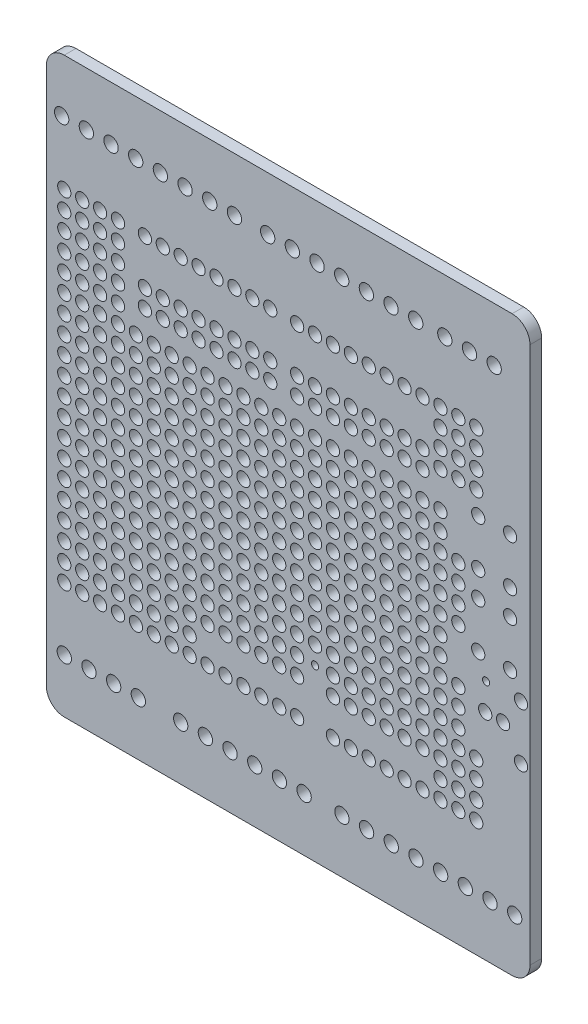
SolidWorks part; units mm, degrees
ref_plane "Front Plane" through (0, 0, 0) normal (0, 0, 1) x (1, 0, 0)
ref_plane "Top Plane" through (0, 0, 0) normal (0, 1, 0) x (1, 0, 0)
ref_plane "Right Plane" through (0, 0, 0) normal (1, 0, 0) x (0, 0, -1)
sketch "Model" plane through (0, 0, 0) normal (0, 0, 1) x (1, 0, 0)
  line L0 (2.54, 0) -> (66.04, 0)
  line L1 (68.58, 2.54) -> (68.58, 78.74)
  line L2 (0, 2.54) -> (0, 78.74)
  line L3 (2.54, 81.28) -> (66.04, 81.28)
  line L4 (48.91, 7.62) -> (45.41, 7.62) construction
  line L5 (45.41, 7.62) -> (41.91, 7.62) construction
  line L6 (26.05, 7.62) -> (22.55, 7.62) construction
  line L7 (22.55, 7.62) -> (19.05, 7.62) construction
  line L8 (9.54, 7.62) -> (6.04, 7.62) construction
  line L9 (6.04, 7.62) -> (2.54, 7.62) construction
  line L10 (23.17, 73.66) -> (26.67, 73.66) construction
  line L11 (56.5, 73.66) -> (60, 73.66) construction
  line L12 (60, 73.66) -> (63.5, 73.66) construction
  circle A0 centre (45.41, 7.62) radius 1.016
  circle A1 centre (45.41, 7.62) radius 1.016
  circle A2 centre (48.91, 7.62) radius 1.016
  circle A3 centre (48.91, 7.62) radius 1.016
  circle A4 centre (52.41, 7.62) radius 1.016
  circle A5 centre (52.41, 7.62) radius 1.016
  circle A6 centre (55.91, 7.62) radius 1.016
  circle A7 centre (55.91, 7.62) radius 1.016
  circle A8 centre (59.41, 7.62) radius 1.016
  circle A9 centre (59.41, 7.62) radius 1.016
  circle A10 centre (62.91, 7.62) radius 1.016
  circle A11 centre (62.91, 7.62) radius 1.016
  circle A12 centre (66.41, 7.62) radius 1.016
  circle A13 centre (66.41, 7.62) radius 1.016
  circle A14 centre (22.55, 7.62) radius 1.016
  circle A15 centre (22.55, 7.62) radius 1.016
  circle A16 centre (26.05, 7.62) radius 1.016
  circle A17 centre (26.05, 7.62) radius 1.016
  circle A18 centre (29.55, 7.62) radius 1.016
  circle A19 centre (29.55, 7.62) radius 1.016
  circle A20 centre (33.05, 7.62) radius 1.016
  circle A21 centre (33.05, 7.62) radius 1.016
  circle A22 centre (36.55, 7.62) radius 1.016
  circle A23 centre (36.55, 7.62) radius 1.016
  circle A24 centre (6.04, 7.62) radius 1.016
  circle A25 centre (6.04, 7.62) radius 1.016
  circle A26 centre (9.54, 7.62) radius 1.016
  circle A27 centre (9.54, 7.62) radius 1.016
  circle A28 centre (13.04, 7.62) radius 1.016
  circle A29 centre (13.04, 7.62) radius 1.016
  circle A30 centre (52.38, 73.66) radius 1.016
  circle A31 centre (52.38, 73.66) radius 1.016
  circle A32 centre (48.88, 73.66) radius 1.016
  circle A33 centre (48.88, 73.66) radius 1.016
  circle A34 centre (45.38, 73.66) radius 1.016
  circle A35 centre (45.38, 73.66) radius 1.016
  circle A36 centre (41.88, 73.66) radius 1.016
  circle A37 centre (41.88, 73.66) radius 1.016
  circle A38 centre (38.38, 73.66) radius 1.016
  circle A39 centre (38.38, 73.66) radius 1.016
  circle A40 centre (34.88, 73.66) radius 1.016
  circle A41 centre (34.88, 73.66) radius 1.016
  circle A42 centre (31.38, 73.66) radius 1.016
  circle A43 centre (31.38, 73.66) radius 1.016
  circle A44 centre (23.17, 73.66) radius 1.016
  circle A45 centre (23.17, 73.66) radius 1.016
  circle A46 centre (19.67, 73.66) radius 1.016
  circle A47 centre (19.67, 73.66) radius 1.016
  circle A48 centre (16.17, 73.66) radius 1.016
  circle A49 centre (16.17, 73.66) radius 1.016
  circle A50 centre (12.67, 73.66) radius 1.016
  circle A51 centre (12.67, 73.66) radius 1.016
  circle A52 centre (9.17, 73.66) radius 1.016
  circle A53 centre (9.17, 73.66) radius 1.016
  circle A54 centre (5.67, 73.66) radius 1.016
  circle A55 centre (5.67, 73.66) radius 1.016
  circle A56 centre (2.17, 73.66) radius 1.016
  circle A57 centre (2.17, 73.66) radius 1.016
  circle A58 centre (60, 73.66) radius 1.016
  circle A59 centre (60, 73.66) radius 1.016
  circle A60 centre (62.23, 30.48) radius 0.9398
  circle A61 centre (62.23, 30.48) radius 0.9398
  circle A62 centre (64.77, 30.48) radius 0.9398
  circle A63 centre (64.77, 30.48) radius 0.9398
  circle A64 centre (67.31, 26.67) radius 0.9398
  circle A65 centre (67.31, 26.67) radius 0.9398
  circle A66 centre (67.31, 34.29) radius 0.9398
  circle A67 centre (67.31, 34.29) radius 0.9398
  circle A68 centre (65.7606, 43.8912) radius 0.9398
  circle A69 centre (65.7606, 43.8912) radius 0.9398
  circle A70 centre (65.7606, 37.3888) radius 0.9398
  circle A71 centre (65.7606, 37.3888) radius 0.9398
  circle A72 centre (61.2394, 43.8912) radius 0.9398
  circle A73 centre (61.2394, 43.8912) radius 0.9398
  circle A74 centre (61.2394, 37.3888) radius 0.9398
  circle A75 centre (61.2394, 37.3888) radius 0.9398
  circle A76 centre (65.7606, 54.0512) radius 0.9398
  circle A77 centre (65.7606, 54.0512) radius 0.9398
  circle A78 centre (65.7606, 47.5488) radius 0.9398
  circle A79 centre (65.7606, 47.5488) radius 0.9398
  circle A80 centre (61.2394, 54.0512) radius 0.9398
  circle A81 centre (61.2394, 54.0512) radius 0.9398
  circle A82 centre (61.2394, 47.5488) radius 0.9398
  circle A83 centre (61.2394, 47.5488) radius 0.9398
  circle A84 centre (25.4, 16.51) radius 0.9398
  circle A85 centre (25.4, 16.51) radius 0.9398
  circle A86 centre (27.94, 16.51) radius 0.9398
  circle A87 centre (27.94, 16.51) radius 0.9398
  circle A88 centre (40.64, 16.51) radius 0.9398
  circle A89 centre (40.64, 16.51) radius 0.9398
  circle A90 centre (43.18, 16.51) radius 0.9398
  circle A91 centre (43.18, 16.51) radius 0.9398
  circle A92 centre (45.72, 16.51) radius 0.9398
  circle A93 centre (45.72, 16.51) radius 0.9398
  circle A94 centre (48.26, 16.51) radius 0.9398
  circle A95 centre (48.26, 16.51) radius 0.9398
  circle A96 centre (50.8, 16.51) radius 0.9398
  circle A97 centre (50.8, 16.51) radius 0.9398
  circle A98 centre (53.34, 16.51) radius 0.9398
  circle A99 centre (53.34, 16.51) radius 0.9398
  circle A100 centre (13.97, 64.77) radius 0.9398
  circle A101 centre (13.97, 64.77) radius 0.9398
  circle A102 centre (48.26, 64.77) radius 0.9398
  circle A103 centre (48.26, 64.77) radius 0.9398
  circle A104 centre (45.72, 64.77) radius 0.9398
  circle A105 centre (45.72, 64.77) radius 0.9398
  circle A106 centre (43.18, 64.77) radius 0.9398
  circle A107 centre (43.18, 64.77) radius 0.9398
  circle A108 centre (40.64, 64.77) radius 0.9398
  circle A109 centre (40.64, 64.77) radius 0.9398
  circle A110 centre (38.1, 64.77) radius 0.9398
  circle A111 centre (38.1, 64.77) radius 0.9398
  circle A112 centre (35.56, 64.77) radius 0.9398
  circle A113 centre (35.56, 64.77) radius 0.9398
  circle A114 centre (31.75, 64.77) radius 0.9398
  circle A115 centre (31.75, 64.77) radius 0.9398
  circle A116 centre (29.21, 64.77) radius 0.9398
  circle A117 centre (29.21, 64.77) radius 0.9398
  circle A118 centre (26.67, 64.77) radius 0.9398
  circle A119 centre (26.67, 64.77) radius 0.9398
  circle A120 centre (24.13, 64.77) radius 0.9398
  circle A121 centre (24.13, 64.77) radius 0.9398
  circle A122 centre (21.59, 64.77) radius 0.9398
  circle A123 centre (21.59, 64.77) radius 0.9398
  circle A124 centre (19.05, 64.77) radius 0.9398
  circle A125 centre (19.05, 64.77) radius 0.9398
  circle A126 centre (30.48, 16.51) radius 0.9398
  circle A127 centre (30.48, 16.51) radius 0.9398
  circle A128 centre (33.02, 16.51) radius 0.9398
  circle A129 centre (33.02, 16.51) radius 0.9398
  circle A130 centre (16.51, 64.77) radius 0.9398
  circle A131 centre (16.51, 64.77) radius 0.9398
  circle A132 centre (22.86, 16.51) radius 0.9398
  circle A133 centre (22.86, 16.51) radius 0.9398
  circle A134 centre (53.34, 64.77) radius 0.9398
  circle A135 centre (53.34, 64.77) radius 0.9398
  circle A136 centre (50.8, 64.77) radius 0.9398
  circle A137 centre (50.8, 64.77) radius 0.9398
  circle A138 centre (35.56, 16.51) radius 0.9398
  circle A139 centre (35.56, 16.51) radius 0.9398
  circle A140 centre (25.4, 24.13) radius 0.9398
  circle A141 centre (25.4, 24.13) radius 0.9398
  circle A142 centre (25.4, 21.59) radius 0.9398
  circle A143 centre (25.4, 21.59) radius 0.9398
  circle A144 centre (45.72, 34.29) radius 0.9398
  circle A145 centre (45.72, 34.29) radius 0.9398
  circle A146 centre (48.26, 34.29) radius 0.9398
  circle A147 centre (48.26, 34.29) radius 0.9398
  circle A148 centre (50.8, 34.29) radius 0.9398
  circle A149 centre (50.8, 34.29) radius 0.9398
  circle A150 centre (53.34, 34.29) radius 0.9398
  circle A151 centre (53.34, 34.29) radius 0.9398
  circle A152 centre (55.88, 34.29) radius 0.9398
  circle A153 centre (55.88, 34.29) radius 0.9398
  circle A154 centre (43.18, 34.29) radius 0.9398
  circle A155 centre (43.18, 34.29) radius 0.9398
  circle A156 centre (40.64, 34.29) radius 0.9398
  circle A157 centre (40.64, 34.29) radius 0.9398
  circle A158 centre (38.1, 34.29) radius 0.9398
  circle A159 centre (38.1, 34.29) radius 0.9398
  circle A160 centre (35.56, 34.29) radius 0.9398
  circle A161 centre (35.56, 34.29) radius 0.9398
  circle A162 centre (33.02, 34.29) radius 0.9398
  circle A163 centre (33.02, 34.29) radius 0.9398
  circle A164 centre (30.48, 34.29) radius 0.9398
  circle A165 centre (30.48, 34.29) radius 0.9398
  circle A166 centre (27.94, 34.29) radius 0.9398
  circle A167 centre (27.94, 34.29) radius 0.9398
  circle A168 centre (25.4, 34.29) radius 0.9398
  circle A169 centre (25.4, 34.29) radius 0.9398
  circle A170 centre (22.86, 34.29) radius 0.9398
  circle A171 centre (22.86, 34.29) radius 0.9398
  circle A172 centre (17.78, 34.29) radius 0.9398
  circle A173 centre (17.78, 34.29) radius 0.9398
  circle A174 centre (20.32, 34.29) radius 0.9398
  circle A175 centre (20.32, 34.29) radius 0.9398
  circle A176 centre (27.94, 24.13) radius 0.9398
  circle A177 centre (27.94, 24.13) radius 0.9398
  circle A178 centre (45.72, 49.53) radius 0.9398
  circle A179 centre (45.72, 49.53) radius 0.9398
  circle A180 centre (48.26, 49.53) radius 0.9398
  circle A181 centre (48.26, 49.53) radius 0.9398
  circle A182 centre (50.8, 49.53) radius 0.9398
  circle A183 centre (50.8, 49.53) radius 0.9398
  circle A184 centre (53.34, 49.53) radius 0.9398
  circle A185 centre (53.34, 49.53) radius 0.9398
  circle A186 centre (55.88, 49.53) radius 0.9398
  circle A187 centre (55.88, 49.53) radius 0.9398
  circle A188 centre (43.18, 49.53) radius 0.9398
  circle A189 centre (43.18, 49.53) radius 0.9398
  circle A190 centre (40.64, 49.53) radius 0.9398
  circle A191 centre (40.64, 49.53) radius 0.9398
  circle A192 centre (38.1, 49.53) radius 0.9398
  circle A193 centre (38.1, 49.53) radius 0.9398
  circle A194 centre (35.56, 49.53) radius 0.9398
  circle A195 centre (35.56, 49.53) radius 0.9398
  circle A196 centre (33.02, 49.53) radius 0.9398
  circle A197 centre (33.02, 49.53) radius 0.9398
  circle A198 centre (30.48, 49.53) radius 0.9398
  circle A199 centre (30.48, 49.53) radius 0.9398
  circle A200 centre (27.94, 49.53) radius 0.9398
  circle A201 centre (27.94, 49.53) radius 0.9398
  circle A202 centre (25.4, 49.53) radius 0.9398
  circle A203 centre (25.4, 49.53) radius 0.9398
  circle A204 centre (22.86, 49.53) radius 0.9398
  circle A205 centre (22.86, 49.53) radius 0.9398
  circle A206 centre (17.78, 49.53) radius 0.9398
  circle A207 centre (17.78, 49.53) radius 0.9398
  circle A208 centre (20.32, 49.53) radius 0.9398
  circle A209 centre (20.32, 49.53) radius 0.9398
  circle A210 centre (15.24, 49.53) radius 0.9398
  circle A211 centre (15.24, 49.53) radius 0.9398
  circle A212 centre (12.7, 49.53) radius 0.9398
  circle A213 centre (12.7, 49.53) radius 0.9398
  circle A214 centre (10.16, 49.53) radius 0.9398
  circle A215 centre (10.16, 49.53) radius 0.9398
  circle A216 centre (7.62, 49.53) radius 0.9398
  circle A217 centre (7.62, 49.53) radius 0.9398
  circle A218 centre (5.08, 49.53) radius 0.9398
  circle A219 centre (5.08, 49.53) radius 0.9398
  circle A220 centre (2.54, 49.53) radius 0.9398
  circle A221 centre (2.54, 49.53) radius 0.9398
  circle A222 centre (27.94, 21.59) radius 0.9398
  circle A223 centre (27.94, 21.59) radius 0.9398
  circle A224 centre (40.64, 21.59) radius 0.9398
  circle A225 centre (40.64, 21.59) radius 0.9398
  circle A226 centre (40.64, 24.13) radius 0.9398
  circle A227 centre (40.64, 24.13) radius 0.9398
  circle A228 centre (43.18, 24.13) radius 0.9398
  circle A229 centre (43.18, 24.13) radius 0.9398
  circle A230 centre (43.18, 21.59) radius 0.9398
  circle A231 centre (43.18, 21.59) radius 0.9398
  circle A232 centre (45.72, 21.59) radius 0.9398
  circle A233 centre (45.72, 21.59) radius 0.9398
  circle A234 centre (45.72, 24.13) radius 0.9398
  circle A235 centre (45.72, 24.13) radius 0.9398
  circle A236 centre (48.26, 24.13) radius 0.9398
  circle A237 centre (48.26, 24.13) radius 0.9398
  circle A238 centre (48.26, 21.59) radius 0.9398
  circle A239 centre (48.26, 21.59) radius 0.9398
  circle A240 centre (50.8, 24.13) radius 0.9398
  circle A241 centre (50.8, 24.13) radius 0.9398
  circle A242 centre (50.8, 21.59) radius 0.9398
  circle A243 centre (50.8, 21.59) radius 0.9398
  circle A244 centre (53.34, 24.13) radius 0.9398
  circle A245 centre (53.34, 24.13) radius 0.9398
  circle A246 centre (53.34, 21.59) radius 0.9398
  circle A247 centre (53.34, 21.59) radius 0.9398
  circle A248 centre (13.97, 55.88) radius 0.9398
  circle A249 centre (13.97, 55.88) radius 0.9398
  circle A250 centre (13.97, 58.42) radius 0.9398
  circle A251 centre (13.97, 58.42) radius 0.9398
  circle A252 centre (5.08, 29.21) radius 0.9398
  circle A253 centre (5.08, 29.21) radius 0.9398
  circle A254 centre (5.08, 31.75) radius 0.9398
  circle A255 centre (5.08, 31.75) radius 0.9398
  circle A256 centre (5.08, 26.67) radius 0.9398
  circle A257 centre (5.08, 26.67) radius 0.9398
  circle A258 centre (7.62, 31.75) radius 0.9398
  circle A259 centre (7.62, 31.75) radius 0.9398
  circle A260 centre (7.62, 26.67) radius 0.9398
  circle A261 centre (7.62, 26.67) radius 0.9398
  circle A262 centre (7.62, 29.21) radius 0.9398
  circle A263 centre (7.62, 29.21) radius 0.9398
  circle A264 centre (10.16, 29.21) radius 0.9398
  circle A265 centre (10.16, 29.21) radius 0.9398
  circle A266 centre (10.16, 31.75) radius 0.9398
  circle A267 centre (10.16, 31.75) radius 0.9398
  circle A268 centre (10.16, 26.67) radius 0.9398
  circle A269 centre (10.16, 26.67) radius 0.9398
  circle A270 centre (12.7, 31.75) radius 0.9398
  circle A271 centre (12.7, 31.75) radius 0.9398
  circle A272 centre (12.7, 29.21) radius 0.9398
  circle A273 centre (12.7, 29.21) radius 0.9398
  circle A274 centre (12.7, 26.67) radius 0.9398
  circle A275 centre (12.7, 26.67) radius 0.9398
  circle A276 centre (15.24, 26.67) radius 0.9398
  circle A277 centre (15.24, 26.67) radius 0.9398
  circle A278 centre (15.24, 29.21) radius 0.9398
  circle A279 centre (15.24, 29.21) radius 0.9398
  circle A280 centre (15.24, 31.75) radius 0.9398
  circle A281 centre (15.24, 31.75) radius 0.9398
  circle A282 centre (17.78, 26.67) radius 0.9398
  circle A283 centre (17.78, 26.67) radius 0.9398
  circle A284 centre (17.78, 29.21) radius 0.9398
  circle A285 centre (17.78, 29.21) radius 0.9398
  circle A286 centre (17.78, 31.75) radius 0.9398
  circle A287 centre (17.78, 31.75) radius 0.9398
  circle A288 centre (20.32, 26.67) radius 0.9398
  circle A289 centre (20.32, 26.67) radius 0.9398
  circle A290 centre (20.32, 29.21) radius 0.9398
  circle A291 centre (20.32, 29.21) radius 0.9398
  circle A292 centre (20.32, 31.75) radius 0.9398
  circle A293 centre (20.32, 31.75) radius 0.9398
  circle A294 centre (22.86, 26.67) radius 0.9398
  circle A295 centre (22.86, 26.67) radius 0.9398
  circle A296 centre (22.86, 29.21) radius 0.9398
  circle A297 centre (22.86, 29.21) radius 0.9398
  circle A298 centre (22.86, 31.75) radius 0.9398
  circle A299 centre (22.86, 31.75) radius 0.9398
  circle A300 centre (25.4, 26.67) radius 0.9398
  circle A301 centre (25.4, 26.67) radius 0.9398
  circle A302 centre (25.4, 29.21) radius 0.9398
  circle A303 centre (25.4, 29.21) radius 0.9398
  circle A304 centre (25.4, 31.75) radius 0.9398
  circle A305 centre (25.4, 31.75) radius 0.9398
  circle A306 centre (27.94, 26.67) radius 0.9398
  circle A307 centre (27.94, 26.67) radius 0.9398
  circle A308 centre (27.94, 29.21) radius 0.9398
  circle A309 centre (27.94, 29.21) radius 0.9398
  circle A310 centre (27.94, 31.75) radius 0.9398
  circle A311 centre (27.94, 31.75) radius 0.9398
  circle A312 centre (30.48, 26.67) radius 0.9398
  circle A313 centre (30.48, 26.67) radius 0.9398
  circle A314 centre (30.48, 29.21) radius 0.9398
  circle A315 centre (30.48, 29.21) radius 0.9398
  circle A316 centre (30.48, 31.75) radius 0.9398
  circle A317 centre (30.48, 31.75) radius 0.9398
  circle A318 centre (33.02, 26.67) radius 0.9398
  circle A319 centre (33.02, 26.67) radius 0.9398
  circle A320 centre (33.02, 29.21) radius 0.9398
  circle A321 centre (33.02, 29.21) radius 0.9398
  circle A322 centre (33.02, 31.75) radius 0.9398
  circle A323 centre (33.02, 31.75) radius 0.9398
  circle A324 centre (35.56, 26.67) radius 0.9398
  circle A325 centre (35.56, 26.67) radius 0.9398
  circle A326 centre (35.56, 29.21) radius 0.9398
  circle A327 centre (35.56, 29.21) radius 0.9398
  circle A328 centre (35.56, 31.75) radius 0.9398
  circle A329 centre (35.56, 31.75) radius 0.9398
  circle A330 centre (38.1, 26.67) radius 0.9398
  circle A331 centre (38.1, 26.67) radius 0.9398
  circle A332 centre (38.1, 29.21) radius 0.9398
  circle A333 centre (38.1, 29.21) radius 0.9398
  circle A334 centre (38.1, 31.75) radius 0.9398
  circle A335 centre (38.1, 31.75) radius 0.9398
  circle A336 centre (40.64, 26.67) radius 0.9398
  circle A337 centre (40.64, 26.67) radius 0.9398
  circle A338 centre (40.64, 29.21) radius 0.9398
  circle A339 centre (40.64, 29.21) radius 0.9398
  circle A340 centre (40.64, 31.75) radius 0.9398
  circle A341 centre (40.64, 31.75) radius 0.9398
  circle A342 centre (43.18, 26.67) radius 0.9398
  circle A343 centre (43.18, 26.67) radius 0.9398
  circle A344 centre (43.18, 29.21) radius 0.9398
  circle A345 centre (43.18, 29.21) radius 0.9398
  circle A346 centre (43.18, 31.75) radius 0.9398
  circle A347 centre (43.18, 31.75) radius 0.9398
  circle A348 centre (45.72, 26.67) radius 0.9398
  circle A349 centre (45.72, 26.67) radius 0.9398
  circle A350 centre (45.72, 29.21) radius 0.9398
  circle A351 centre (45.72, 29.21) radius 0.9398
  circle A352 centre (45.72, 31.75) radius 0.9398
  circle A353 centre (45.72, 31.75) radius 0.9398
  circle A354 centre (48.26, 26.67) radius 0.9398
  circle A355 centre (48.26, 26.67) radius 0.9398
  circle A356 centre (48.26, 29.21) radius 0.9398
  circle A357 centre (48.26, 29.21) radius 0.9398
  circle A358 centre (48.26, 31.75) radius 0.9398
  circle A359 centre (48.26, 31.75) radius 0.9398
  circle A360 centre (50.8, 26.67) radius 0.9398
  circle A361 centre (50.8, 26.67) radius 0.9398
  circle A362 centre (50.8, 29.21) radius 0.9398
  circle A363 centre (50.8, 29.21) radius 0.9398
  circle A364 centre (50.8, 31.75) radius 0.9398
  circle A365 centre (50.8, 31.75) radius 0.9398
  circle A366 centre (53.34, 26.67) radius 0.9398
  circle A367 centre (53.34, 26.67) radius 0.9398
  circle A368 centre (53.34, 29.21) radius 0.9398
  circle A369 centre (53.34, 29.21) radius 0.9398
  circle A370 centre (53.34, 31.75) radius 0.9398
  circle A371 centre (53.34, 31.75) radius 0.9398
  circle A372 centre (55.88, 29.21) radius 0.9398
  circle A373 centre (55.88, 29.21) radius 0.9398
  circle A374 centre (15.24, 46.99) radius 0.9398
  circle A375 centre (15.24, 46.99) radius 0.9398
  circle A376 centre (12.7, 46.99) radius 0.9398
  circle A377 centre (12.7, 46.99) radius 0.9398
  circle A378 centre (15.24, 44.45) radius 0.9398
  circle A379 centre (15.24, 44.45) radius 0.9398
  circle A380 centre (15.24, 41.91) radius 0.9398
  circle A381 centre (15.24, 41.91) radius 0.9398
  circle A382 centre (12.7, 44.45) radius 0.9398
  circle A383 centre (12.7, 44.45) radius 0.9398
  circle A384 centre (10.16, 46.99) radius 0.9398
  circle A385 centre (10.16, 46.99) radius 0.9398
  circle A386 centre (7.62, 46.99) radius 0.9398
  circle A387 centre (7.62, 46.99) radius 0.9398
  circle A388 centre (10.16, 44.45) radius 0.9398
  circle A389 centre (10.16, 44.45) radius 0.9398
  circle A390 centre (12.7, 41.91) radius 0.9398
  circle A391 centre (12.7, 41.91) radius 0.9398
  circle A392 centre (15.24, 39.37) radius 0.9398
  circle A393 centre (15.24, 39.37) radius 0.9398
  circle A394 centre (15.24, 36.83) radius 0.9398
  circle A395 centre (15.24, 36.83) radius 0.9398
  circle A396 centre (12.7, 39.37) radius 0.9398
  circle A397 centre (12.7, 39.37) radius 0.9398
  circle A398 centre (10.16, 41.91) radius 0.9398
  circle A399 centre (10.16, 41.91) radius 0.9398
  circle A400 centre (7.62, 44.45) radius 0.9398
  circle A401 centre (7.62, 44.45) radius 0.9398
  circle A402 centre (5.08, 46.99) radius 0.9398
  circle A403 centre (5.08, 46.99) radius 0.9398
  circle A404 centre (2.54, 46.99) radius 0.9398
  circle A405 centre (2.54, 46.99) radius 0.9398
  circle A406 centre (5.08, 44.45) radius 0.9398
  circle A407 centre (5.08, 44.45) radius 0.9398
  circle A408 centre (7.62, 41.91) radius 0.9398
  circle A409 centre (7.62, 41.91) radius 0.9398
  circle A410 centre (10.16, 39.37) radius 0.9398
  circle A411 centre (10.16, 39.37) radius 0.9398
  circle A412 centre (12.7, 36.83) radius 0.9398
  circle A413 centre (12.7, 36.83) radius 0.9398
  circle A414 centre (15.24, 34.29) radius 0.9398
  circle A415 centre (15.24, 34.29) radius 0.9398
  circle A416 centre (12.7, 34.29) radius 0.9398
  circle A417 centre (12.7, 34.29) radius 0.9398
  circle A418 centre (10.16, 36.83) radius 0.9398
  circle A419 centre (10.16, 36.83) radius 0.9398
  circle A420 centre (7.62, 39.37) radius 0.9398
  circle A421 centre (7.62, 39.37) radius 0.9398
  circle A422 centre (2.54, 44.45) radius 0.9398
  circle A423 centre (2.54, 44.45) radius 0.9398
  circle A424 centre (5.08, 41.91) radius 0.9398
  circle A425 centre (5.08, 41.91) radius 0.9398
  circle A426 centre (2.54, 41.91) radius 0.9398
  circle A427 centre (2.54, 41.91) radius 0.9398
  circle A428 centre (5.08, 39.37) radius 0.9398
  circle A429 centre (5.08, 39.37) radius 0.9398
  circle A430 centre (7.62, 36.83) radius 0.9398
  circle A431 centre (7.62, 36.83) radius 0.9398
  circle A432 centre (10.16, 34.29) radius 0.9398
  circle A433 centre (10.16, 34.29) radius 0.9398
  circle A434 centre (7.62, 34.29) radius 0.9398
  circle A435 centre (7.62, 34.29) radius 0.9398
  circle A436 centre (2.54, 39.37) radius 0.9398
  circle A437 centre (2.54, 39.37) radius 0.9398
  circle A438 centre (5.08, 36.83) radius 0.9398
  circle A439 centre (5.08, 36.83) radius 0.9398
  circle A440 centre (2.54, 36.83) radius 0.9398
  circle A441 centre (2.54, 36.83) radius 0.9398
  circle A442 centre (5.08, 34.29) radius 0.9398
  circle A443 centre (5.08, 34.29) radius 0.9398
  circle A444 centre (2.54, 34.29) radius 0.9398
  circle A445 centre (2.54, 34.29) radius 0.9398
  circle A446 centre (53.34, 58.42) radius 0.9398
  circle A447 centre (53.34, 58.42) radius 0.9398
  circle A448 centre (53.34, 55.88) radius 0.9398
  circle A449 centre (53.34, 55.88) radius 0.9398
  circle A450 centre (50.8, 58.42) radius 0.9398
  circle A451 centre (50.8, 58.42) radius 0.9398
  circle A452 centre (50.8, 55.88) radius 0.9398
  circle A453 centre (50.8, 55.88) radius 0.9398
  circle A454 centre (48.26, 58.42) radius 0.9398
  circle A455 centre (48.26, 58.42) radius 0.9398
  circle A456 centre (48.26, 55.88) radius 0.9398
  circle A457 centre (48.26, 55.88) radius 0.9398
  circle A458 centre (45.72, 58.42) radius 0.9398
  circle A459 centre (45.72, 58.42) radius 0.9398
  circle A460 centre (45.72, 55.88) radius 0.9398
  circle A461 centre (45.72, 55.88) radius 0.9398
  circle A462 centre (43.18, 58.42) radius 0.9398
  circle A463 centre (43.18, 58.42) radius 0.9398
  circle A464 centre (43.18, 55.88) radius 0.9398
  circle A465 centre (43.18, 55.88) radius 0.9398
  circle A466 centre (40.64, 58.42) radius 0.9398
  circle A467 centre (40.64, 58.42) radius 0.9398
  circle A468 centre (40.64, 55.88) radius 0.9398
  circle A469 centre (40.64, 55.88) radius 0.9398
  circle A470 centre (38.1, 58.42) radius 0.9398
  circle A471 centre (38.1, 58.42) radius 0.9398
  circle A472 centre (38.1, 55.88) radius 0.9398
  circle A473 centre (38.1, 55.88) radius 0.9398
  circle A474 centre (35.56, 58.42) radius 0.9398
  circle A475 centre (35.56, 58.42) radius 0.9398
  circle A476 centre (35.56, 55.88) radius 0.9398
  circle A477 centre (35.56, 55.88) radius 0.9398
  circle A478 centre (31.75, 58.42) radius 0.9398
  circle A479 centre (31.75, 58.42) radius 0.9398
  circle A480 centre (31.75, 55.88) radius 0.9398
  circle A481 centre (31.75, 55.88) radius 0.9398
  circle A482 centre (29.21, 58.42) radius 0.9398
  circle A483 centre (29.21, 58.42) radius 0.9398
  circle A484 centre (29.21, 55.88) radius 0.9398
  circle A485 centre (29.21, 55.88) radius 0.9398
  circle A486 centre (26.67, 58.42) radius 0.9398
  circle A487 centre (26.67, 58.42) radius 0.9398
  circle A488 centre (26.67, 55.88) radius 0.9398
  circle A489 centre (26.67, 55.88) radius 0.9398
  circle A490 centre (24.13, 58.42) radius 0.9398
  circle A491 centre (24.13, 58.42) radius 0.9398
  circle A492 centre (24.13, 55.88) radius 0.9398
  circle A493 centre (24.13, 55.88) radius 0.9398
  circle A494 centre (21.59, 58.42) radius 0.9398
  circle A495 centre (21.59, 58.42) radius 0.9398
  circle A496 centre (21.59, 55.88) radius 0.9398
  circle A497 centre (21.59, 55.88) radius 0.9398
  circle A498 centre (19.05, 58.42) radius 0.9398
  circle A499 centre (19.05, 58.42) radius 0.9398
  circle A500 centre (19.05, 55.88) radius 0.9398
  circle A501 centre (19.05, 55.88) radius 0.9398
  circle A502 centre (16.51, 58.42) radius 0.9398
  circle A503 centre (16.51, 58.42) radius 0.9398
  circle A504 centre (16.51, 55.88) radius 0.9398
  circle A505 centre (16.51, 55.88) radius 0.9398
  circle A506 centre (33.02, 24.13) radius 0.9398
  circle A507 centre (33.02, 24.13) radius 0.9398
  circle A508 centre (55.88, 52.07) radius 0.9398
  circle A509 centre (55.88, 52.07) radius 0.9398
  circle A510 centre (53.34, 52.07) radius 0.9398
  circle A511 centre (53.34, 52.07) radius 0.9398
  circle A512 centre (50.8, 52.07) radius 0.9398
  circle A513 centre (50.8, 52.07) radius 0.9398
  circle A514 centre (48.26, 52.07) radius 0.9398
  circle A515 centre (48.26, 52.07) radius 0.9398
  circle A516 centre (45.72, 52.07) radius 0.9398
  circle A517 centre (45.72, 52.07) radius 0.9398
  circle A518 centre (43.18, 52.07) radius 0.9398
  circle A519 centre (43.18, 52.07) radius 0.9398
  circle A520 centre (40.64, 52.07) radius 0.9398
  circle A521 centre (40.64, 52.07) radius 0.9398
  circle A522 centre (38.1, 52.07) radius 0.9398
  circle A523 centre (38.1, 52.07) radius 0.9398
  circle A524 centre (35.56, 52.07) radius 0.9398
  circle A525 centre (35.56, 52.07) radius 0.9398
  circle A526 centre (33.02, 52.07) radius 0.9398
  circle A527 centre (33.02, 52.07) radius 0.9398
  circle A528 centre (30.48, 52.07) radius 0.9398
  circle A529 centre (30.48, 52.07) radius 0.9398
  circle A530 centre (27.94, 52.07) radius 0.9398
  circle A531 centre (27.94, 52.07) radius 0.9398
  circle A532 centre (25.4, 52.07) radius 0.9398
  circle A533 centre (25.4, 52.07) radius 0.9398
  circle A534 centre (22.86, 52.07) radius 0.9398
  circle A535 centre (22.86, 52.07) radius 0.9398
  circle A536 centre (20.32, 52.07) radius 0.9398
  circle A537 centre (20.32, 52.07) radius 0.9398
  circle A538 centre (17.78, 52.07) radius 0.9398
  circle A539 centre (17.78, 52.07) radius 0.9398
  circle A540 centre (15.24, 52.07) radius 0.9398
  circle A541 centre (15.24, 52.07) radius 0.9398
  circle A542 centre (12.7, 52.07) radius 0.9398
  circle A543 centre (12.7, 52.07) radius 0.9398
  circle A544 centre (10.16, 52.07) radius 0.9398
  circle A545 centre (10.16, 52.07) radius 0.9398
  circle A546 centre (7.62, 52.07) radius 0.9398
  circle A547 centre (7.62, 52.07) radius 0.9398
  circle A548 centre (5.08, 52.07) radius 0.9398
  circle A549 centre (5.08, 52.07) radius 0.9398
  circle A550 centre (2.54, 52.07) radius 0.9398
  circle A551 centre (2.54, 52.07) radius 0.9398
  circle A552 centre (30.48, 21.59) radius 0.9398
  circle A553 centre (30.48, 21.59) radius 0.9398
  circle A554 centre (30.48, 24.13) radius 0.9398
  circle A555 centre (30.48, 24.13) radius 0.9398
  circle A556 centre (33.02, 21.59) radius 0.9398
  circle A557 centre (33.02, 21.59) radius 0.9398
  circle A558 centre (55.88, 36.83) radius 0.9398
  circle A559 centre (55.88, 36.83) radius 0.9398
  circle A560 centre (53.34, 36.83) radius 0.9398
  circle A561 centre (53.34, 36.83) radius 0.9398
  circle A562 centre (50.8, 36.83) radius 0.9398
  circle A563 centre (50.8, 36.83) radius 0.9398
  circle A564 centre (48.26, 36.83) radius 0.9398
  circle A565 centre (48.26, 36.83) radius 0.9398
  circle A566 centre (45.72, 36.83) radius 0.9398
  circle A567 centre (45.72, 36.83) radius 0.9398
  circle A568 centre (43.18, 36.83) radius 0.9398
  circle A569 centre (43.18, 36.83) radius 0.9398
  circle A570 centre (40.64, 36.83) radius 0.9398
  circle A571 centre (40.64, 36.83) radius 0.9398
  circle A572 centre (38.1, 36.83) radius 0.9398
  circle A573 centre (38.1, 36.83) radius 0.9398
  circle A574 centre (35.56, 36.83) radius 0.9398
  circle A575 centre (35.56, 36.83) radius 0.9398
  circle A576 centre (33.02, 36.83) radius 0.9398
  circle A577 centre (33.02, 36.83) radius 0.9398
  circle A578 centre (30.48, 36.83) radius 0.9398
  circle A579 centre (30.48, 36.83) radius 0.9398
  circle A580 centre (27.94, 36.83) radius 0.9398
  circle A581 centre (27.94, 36.83) radius 0.9398
  circle A582 centre (25.4, 36.83) radius 0.9398
  circle A583 centre (25.4, 36.83) radius 0.9398
  circle A584 centre (22.86, 36.83) radius 0.9398
  circle A585 centre (22.86, 36.83) radius 0.9398
  circle A586 centre (20.32, 36.83) radius 0.9398
  circle A587 centre (20.32, 36.83) radius 0.9398
  circle A588 centre (17.78, 36.83) radius 0.9398
  circle A589 centre (17.78, 36.83) radius 0.9398
  circle A590 centre (55.88, 31.75) radius 0.9398
  circle A591 centre (55.88, 31.75) radius 0.9398
  circle A592 centre (55.88, 26.67) radius 0.9398
  circle A593 centre (55.88, 26.67) radius 0.9398
  circle A594 centre (2.54, 16.51) radius 0.9398
  circle A595 centre (2.54, 16.51) radius 0.9398
  circle A596 centre (2.54, 19.05) radius 0.9398
  circle A597 centre (2.54, 19.05) radius 0.9398
  circle A598 centre (2.54, 24.13) radius 0.9398
  circle A599 centre (2.54, 24.13) radius 0.9398
  circle A600 centre (2.54, 21.59) radius 0.9398
  circle A601 centre (2.54, 21.59) radius 0.9398
  circle A602 centre (5.08, 24.13) radius 0.9398
  circle A603 centre (5.08, 24.13) radius 0.9398
  circle A604 centre (5.08, 59.69) radius 0.9398
  circle A605 centre (5.08, 59.69) radius 0.9398
  circle A606 centre (5.08, 57.15) radius 0.9398
  circle A607 centre (5.08, 57.15) radius 0.9398
  circle A608 centre (7.62, 57.15) radius 0.9398
  circle A609 centre (7.62, 57.15) radius 0.9398
  circle A610 centre (7.62, 59.69) radius 0.9398
  circle A611 centre (7.62, 59.69) radius 0.9398
  circle A612 centre (10.16, 59.69) radius 0.9398
  circle A613 centre (10.16, 59.69) radius 0.9398
  circle A614 centre (10.16, 57.15) radius 0.9398
  circle A615 centre (10.16, 57.15) radius 0.9398
  circle A616 centre (7.62, 24.13) radius 0.9398
  circle A617 centre (7.62, 24.13) radius 0.9398
  circle A618 centre (10.16, 24.13) radius 0.9398
  circle A619 centre (10.16, 24.13) radius 0.9398
  circle A620 centre (12.7, 24.13) radius 0.9398
  circle A621 centre (12.7, 24.13) radius 0.9398
  circle A622 centre (15.24, 24.13) radius 0.9398
  circle A623 centre (15.24, 24.13) radius 0.9398
  circle A624 centre (17.78, 24.13) radius 0.9398
  circle A625 centre (17.78, 24.13) radius 0.9398
  circle A626 centre (20.32, 24.13) radius 0.9398
  circle A627 centre (20.32, 24.13) radius 0.9398
  circle A628 centre (5.08, 21.59) radius 0.9398
  circle A629 centre (5.08, 21.59) radius 0.9398
  circle A630 centre (7.62, 21.59) radius 0.9398
  circle A631 centre (7.62, 21.59) radius 0.9398
  circle A632 centre (10.16, 21.59) radius 0.9398
  circle A633 centre (10.16, 21.59) radius 0.9398
  circle A634 centre (12.7, 21.59) radius 0.9398
  circle A635 centre (12.7, 21.59) radius 0.9398
  circle A636 centre (15.24, 21.59) radius 0.9398
  circle A637 centre (15.24, 21.59) radius 0.9398
  circle A638 centre (17.78, 21.59) radius 0.9398
  circle A639 centre (17.78, 21.59) radius 0.9398
  circle A640 centre (20.32, 21.59) radius 0.9398
  circle A641 centre (20.32, 21.59) radius 0.9398
  circle A642 centre (55.88, 24.13) radius 0.9398
  circle A643 centre (55.88, 24.13) radius 0.9398
  circle A644 centre (58.42, 24.13) radius 0.9398
  circle A645 centre (58.42, 24.13) radius 0.9398
  circle A646 centre (60.96, 24.13) radius 0.9398
  circle A647 centre (60.96, 24.13) radius 0.9398
  circle A648 centre (55.88, 21.59) radius 0.9398
  circle A649 centre (55.88, 21.59) radius 0.9398
  circle A650 centre (58.42, 21.59) radius 0.9398
  circle A651 centre (58.42, 21.59) radius 0.9398
  circle A652 centre (60.96, 21.59) radius 0.9398
  circle A653 centre (60.96, 21.59) radius 0.9398
  circle A654 centre (55.88, 59.69) radius 0.9398
  circle A655 centre (55.88, 59.69) radius 0.9398
  circle A656 centre (58.42, 59.69) radius 0.9398
  circle A657 centre (58.42, 59.69) radius 0.9398
  circle A658 centre (60.96, 59.69) radius 0.9398
  circle A659 centre (60.96, 59.69) radius 0.9398
  circle A660 centre (55.88, 57.15) radius 0.9398
  circle A661 centre (55.88, 57.15) radius 0.9398
  circle A662 centre (58.42, 57.15) radius 0.9398
  circle A663 centre (58.42, 57.15) radius 0.9398
  circle A664 centre (60.96, 57.15) radius 0.9398
  circle A665 centre (60.96, 57.15) radius 0.9398
  circle A666 centre (2.54, 26.67) radius 0.9398
  circle A667 centre (2.54, 26.67) radius 0.9398
  circle A668 centre (58.42, 26.67) radius 0.9398
  circle A669 centre (58.42, 26.67) radius 0.9398
  circle A670 centre (2.54, 29.21) radius 0.9398
  circle A671 centre (2.54, 29.21) radius 0.9398
  circle A672 centre (58.42, 29.21) radius 0.9398
  circle A673 centre (58.42, 29.21) radius 0.9398
  circle A674 centre (2.54, 31.75) radius 0.9398
  circle A675 centre (2.54, 31.75) radius 0.9398
  circle A676 centre (58.42, 31.75) radius 0.9398
  circle A677 centre (58.42, 31.75) radius 0.9398
  circle A678 centre (17.78, 39.37) radius 0.9398
  circle A679 centre (17.78, 39.37) radius 0.9398
  circle A680 centre (20.32, 39.37) radius 0.9398
  circle A681 centre (20.32, 39.37) radius 0.9398
  circle A682 centre (22.86, 39.37) radius 0.9398
  circle A683 centre (22.86, 39.37) radius 0.9398
  circle A684 centre (25.4, 39.37) radius 0.9398
  circle A685 centre (25.4, 39.37) radius 0.9398
  circle A686 centre (27.94, 39.37) radius 0.9398
  circle A687 centre (27.94, 39.37) radius 0.9398
  circle A688 centre (30.48, 39.37) radius 0.9398
  circle A689 centre (30.48, 39.37) radius 0.9398
  circle A690 centre (33.02, 39.37) radius 0.9398
  circle A691 centre (33.02, 39.37) radius 0.9398
  circle A692 centre (35.56, 39.37) radius 0.9398
  circle A693 centre (35.56, 39.37) radius 0.9398
  circle A694 centre (38.1, 39.37) radius 0.9398
  circle A695 centre (38.1, 39.37) radius 0.9398
  circle A696 centre (40.64, 39.37) radius 0.9398
  circle A697 centre (40.64, 39.37) radius 0.9398
  circle A698 centre (43.18, 39.37) radius 0.9398
  circle A699 centre (43.18, 39.37) radius 0.9398
  circle A700 centre (45.72, 39.37) radius 0.9398
  circle A701 centre (45.72, 39.37) radius 0.9398
  circle A702 centre (48.26, 39.37) radius 0.9398
  circle A703 centre (48.26, 39.37) radius 0.9398
  circle A704 centre (50.8, 39.37) radius 0.9398
  circle A705 centre (50.8, 39.37) radius 0.9398
  circle A706 centre (53.34, 39.37) radius 0.9398
  circle A707 centre (53.34, 39.37) radius 0.9398
  circle A708 centre (55.88, 39.37) radius 0.9398
  circle A709 centre (55.88, 39.37) radius 0.9398
  circle A710 centre (58.42, 39.37) radius 0.9398
  circle A711 centre (58.42, 39.37) radius 0.9398
  circle A712 centre (17.78, 41.91) radius 0.9398
  circle A713 centre (17.78, 41.91) radius 0.9398
  circle A714 centre (20.32, 41.91) radius 0.9398
  circle A715 centre (20.32, 41.91) radius 0.9398
  circle A716 centre (22.86, 41.91) radius 0.9398
  circle A717 centre (22.86, 41.91) radius 0.9398
  circle A718 centre (25.4, 41.91) radius 0.9398
  circle A719 centre (25.4, 41.91) radius 0.9398
  circle A720 centre (27.94, 41.91) radius 0.9398
  circle A721 centre (27.94, 41.91) radius 0.9398
  circle A722 centre (30.48, 41.91) radius 0.9398
  circle A723 centre (30.48, 41.91) radius 0.9398
  circle A724 centre (33.02, 41.91) radius 0.9398
  circle A725 centre (33.02, 41.91) radius 0.9398
  circle A726 centre (35.56, 41.91) radius 0.9398
  circle A727 centre (35.56, 41.91) radius 0.9398
  circle A728 centre (38.1, 41.91) radius 0.9398
  circle A729 centre (38.1, 41.91) radius 0.9398
  circle A730 centre (40.64, 41.91) radius 0.9398
  circle A731 centre (40.64, 41.91) radius 0.9398
  circle A732 centre (43.18, 41.91) radius 0.9398
  circle A733 centre (43.18, 41.91) radius 0.9398
  circle A734 centre (45.72, 41.91) radius 0.9398
  circle A735 centre (45.72, 41.91) radius 0.9398
  circle A736 centre (48.26, 41.91) radius 0.9398
  circle A737 centre (48.26, 41.91) radius 0.9398
  circle A738 centre (50.8, 41.91) radius 0.9398
  circle A739 centre (50.8, 41.91) radius 0.9398
  circle A740 centre (53.34, 41.91) radius 0.9398
  circle A741 centre (53.34, 41.91) radius 0.9398
  circle A742 centre (55.88, 41.91) radius 0.9398
  circle A743 centre (55.88, 41.91) radius 0.9398
  circle A744 centre (58.42, 41.91) radius 0.9398
  circle A745 centre (58.42, 41.91) radius 0.9398
  circle A746 centre (17.78, 44.45) radius 0.9398
  circle A747 centre (17.78, 44.45) radius 0.9398
  circle A748 centre (20.32, 44.45) radius 0.9398
  circle A749 centre (20.32, 44.45) radius 0.9398
  circle A750 centre (22.86, 44.45) radius 0.9398
  circle A751 centre (22.86, 44.45) radius 0.9398
  circle A752 centre (25.4, 44.45) radius 0.9398
  circle A753 centre (25.4, 44.45) radius 0.9398
  circle A754 centre (27.94, 44.45) radius 0.9398
  circle A755 centre (27.94, 44.45) radius 0.9398
  circle A756 centre (30.48, 44.45) radius 0.9398
  circle A757 centre (30.48, 44.45) radius 0.9398
  circle A758 centre (33.02, 44.45) radius 0.9398
  circle A759 centre (33.02, 44.45) radius 0.9398
  circle A760 centre (35.56, 44.45) radius 0.9398
  circle A761 centre (35.56, 44.45) radius 0.9398
  circle A762 centre (38.1, 44.45) radius 0.9398
  circle A763 centre (38.1, 44.45) radius 0.9398
  circle A764 centre (40.64, 44.45) radius 0.9398
  circle A765 centre (40.64, 44.45) radius 0.9398
  circle A766 centre (43.18, 44.45) radius 0.9398
  circle A767 centre (43.18, 44.45) radius 0.9398
  circle A768 centre (45.72, 44.45) radius 0.9398
  circle A769 centre (45.72, 44.45) radius 0.9398
  circle A770 centre (48.26, 44.45) radius 0.9398
  circle A771 centre (48.26, 44.45) radius 0.9398
  circle A772 centre (50.8, 44.45) radius 0.9398
  circle A773 centre (50.8, 44.45) radius 0.9398
  circle A774 centre (53.34, 44.45) radius 0.9398
  circle A775 centre (53.34, 44.45) radius 0.9398
  circle A776 centre (55.88, 44.45) radius 0.9398
  circle A777 centre (55.88, 44.45) radius 0.9398
  circle A778 centre (58.42, 44.45) radius 0.9398
  circle A779 centre (58.42, 44.45) radius 0.9398
  circle A780 centre (17.78, 46.99) radius 0.9398
  circle A781 centre (17.78, 46.99) radius 0.9398
  circle A782 centre (20.32, 46.99) radius 0.9398
  circle A783 centre (20.32, 46.99) radius 0.9398
  circle A784 centre (22.86, 46.99) radius 0.9398
  circle A785 centre (22.86, 46.99) radius 0.9398
  circle A786 centre (25.4, 46.99) radius 0.9398
  circle A787 centre (25.4, 46.99) radius 0.9398
  circle A788 centre (27.94, 46.99) radius 0.9398
  circle A789 centre (27.94, 46.99) radius 0.9398
  circle A790 centre (30.48, 46.99) radius 0.9398
  circle A791 centre (30.48, 46.99) radius 0.9398
  circle A792 centre (33.02, 46.99) radius 0.9398
  circle A793 centre (33.02, 46.99) radius 0.9398
  circle A794 centre (35.56, 46.99) radius 0.9398
  circle A795 centre (35.56, 46.99) radius 0.9398
  circle A796 centre (38.1, 46.99) radius 0.9398
  circle A797 centre (38.1, 46.99) radius 0.9398
  circle A798 centre (40.64, 46.99) radius 0.9398
  circle A799 centre (40.64, 46.99) radius 0.9398
  circle A800 centre (43.18, 46.99) radius 0.9398
  circle A801 centre (43.18, 46.99) radius 0.9398
  circle A802 centre (45.72, 46.99) radius 0.9398
  circle A803 centre (45.72, 46.99) radius 0.9398
  circle A804 centre (48.26, 46.99) radius 0.9398
  circle A805 centre (48.26, 46.99) radius 0.9398
  circle A806 centre (50.8, 46.99) radius 0.9398
  circle A807 centre (50.8, 46.99) radius 0.9398
  circle A808 centre (53.34, 46.99) radius 0.9398
  circle A809 centre (53.34, 46.99) radius 0.9398
  circle A810 centre (55.88, 46.99) radius 0.9398
  circle A811 centre (55.88, 46.99) radius 0.9398
  circle A812 centre (58.42, 46.99) radius 0.9398
  circle A813 centre (58.42, 46.99) radius 0.9398
  circle A814 centre (2.54, 54.61) radius 0.9398
  circle A815 centre (2.54, 54.61) radius 0.9398
  circle A816 centre (5.08, 54.61) radius 0.9398
  circle A817 centre (5.08, 54.61) radius 0.9398
  circle A818 centre (7.62, 54.61) radius 0.9398
  circle A819 centre (7.62, 54.61) radius 0.9398
  circle A820 centre (10.16, 54.61) radius 0.9398
  circle A821 centre (10.16, 54.61) radius 0.9398
  circle A822 centre (2.54, 57.15) radius 0.9398
  circle A823 centre (2.54, 57.15) radius 0.9398
  circle A824 centre (2.54, 59.69) radius 0.9398
  circle A825 centre (2.54, 59.69) radius 0.9398
  circle A826 centre (5.08, 19.05) radius 0.9398
  circle A827 centre (5.08, 19.05) radius 0.9398
  circle A828 centre (7.62, 19.05) radius 0.9398
  circle A829 centre (7.62, 19.05) radius 0.9398
  circle A830 centre (10.16, 19.05) radius 0.9398
  circle A831 centre (10.16, 19.05) radius 0.9398
  circle A832 centre (12.7, 19.05) radius 0.9398
  circle A833 centre (12.7, 19.05) radius 0.9398
  circle A834 centre (15.24, 19.05) radius 0.9398
  circle A835 centre (15.24, 19.05) radius 0.9398
  circle A836 centre (17.78, 19.05) radius 0.9398
  circle A837 centre (17.78, 19.05) radius 0.9398
  circle A838 centre (20.32, 19.05) radius 0.9398
  circle A839 centre (20.32, 19.05) radius 0.9398
  circle A840 centre (5.08, 16.51) radius 0.9398
  circle A841 centre (5.08, 16.51) radius 0.9398
  circle A842 centre (7.62, 16.51) radius 0.9398
  circle A843 centre (7.62, 16.51) radius 0.9398
  circle A844 centre (10.16, 16.51) radius 0.9398
  circle A845 centre (10.16, 16.51) radius 0.9398
  circle A846 centre (12.7, 16.51) radius 0.9398
  circle A847 centre (12.7, 16.51) radius 0.9398
  circle A848 centre (15.24, 16.51) radius 0.9398
  circle A849 centre (15.24, 16.51) radius 0.9398
  circle A850 centre (17.78, 16.51) radius 0.9398
  circle A851 centre (17.78, 16.51) radius 0.9398
  circle A852 centre (20.32, 16.51) radius 0.9398
  circle A853 centre (20.32, 16.51) radius 0.9398
  circle A854 centre (2.54, 62.23) radius 0.9398
  circle A855 centre (2.54, 62.23) radius 0.9398
  circle A856 centre (5.08, 62.23) radius 0.9398
  circle A857 centre (5.08, 62.23) radius 0.9398
  circle A858 centre (7.62, 62.23) radius 0.9398
  circle A859 centre (7.62, 62.23) radius 0.9398
  circle A860 centre (55.88, 19.05) radius 0.9398
  circle A861 centre (55.88, 19.05) radius 0.9398
  circle A862 centre (58.42, 19.05) radius 0.9398
  circle A863 centre (58.42, 19.05) radius 0.9398
  circle A864 centre (60.96, 19.05) radius 0.9398
  circle A865 centre (60.96, 19.05) radius 0.9398
  circle A866 centre (10.16, 62.23) radius 0.9398
  circle A867 centre (10.16, 62.23) radius 0.9398
  circle A868 centre (2.54, 64.77) radius 0.9398
  circle A869 centre (2.54, 64.77) radius 0.9398
  circle A870 centre (5.08, 64.77) radius 0.9398
  circle A871 centre (5.08, 64.77) radius 0.9398
  circle A872 centre (7.62, 64.77) radius 0.9398
  circle A873 centre (7.62, 64.77) radius 0.9398
  circle A874 centre (10.16, 64.77) radius 0.9398
  circle A875 centre (10.16, 64.77) radius 0.9398
  circle A876 centre (55.88, 16.51) radius 0.9398
  circle A877 centre (55.88, 16.51) radius 0.9398
  circle A878 centre (58.42, 16.51) radius 0.9398
  circle A879 centre (58.42, 16.51) radius 0.9398
  circle A880 centre (60.96, 16.51) radius 0.9398
  circle A881 centre (60.96, 16.51) radius 0.9398
  circle A882 centre (55.88, 62.23) radius 0.9398
  circle A883 centre (55.88, 62.23) radius 0.9398
  circle A884 centre (58.42, 62.23) radius 0.9398
  circle A885 centre (58.42, 62.23) radius 0.9398
  circle A886 centre (60.96, 62.23) radius 0.9398
  circle A887 centre (60.96, 62.23) radius 0.9398
  circle A888 centre (55.88, 64.77) radius 0.9398
  circle A889 centre (55.88, 64.77) radius 0.9398
  circle A890 centre (58.42, 64.77) radius 0.9398
  circle A891 centre (58.42, 64.77) radius 0.9398
  circle A892 centre (60.96, 64.77) radius 0.9398
  circle A893 centre (60.96, 64.77) radius 0.9398
  circle A894 centre (22.86, 21.59) radius 0.9398
  circle A895 centre (22.86, 21.59) radius 0.9398
  circle A896 centre (22.86, 24.13) radius 0.9398
  circle A897 centre (22.86, 24.13) radius 0.9398
  circle A898 centre (38.1, 24.13) radius 0.508
  circle A899 centre (38.1, 24.13) radius 0.508
  circle A900 centre (62.357, 34.29) radius 0.508
  circle A901 centre (62.357, 34.29) radius 0.508
  circle A902 centre (35.56, 24.13) radius 0.9398
  circle A903 centre (35.56, 24.13) radius 0.9398
  circle A904 centre (35.56, 21.59) radius 0.9398
  circle A905 centre (35.56, 21.59) radius 0.9398
  arc A906 (68.58, 78.74) -> (66.04, 81.28) centre (66.04, 78.74) ccw
  arc A907 (66.04, 0) -> (68.58, 2.54) centre (66.04, 2.54) ccw
  arc A908 (0, 2.54) -> (2.54, 0) centre (2.54, 2.54) ccw
  arc A909 (2.54, 81.28) -> (0, 78.74) centre (2.54, 78.74) ccw
  circle A910 centre (41.91, 7.62) radius 1.016
  circle A911 centre (19.05, 7.62) radius 1.016
  circle A912 centre (2.54, 7.62) radius 1.016
  circle A913 centre (26.67, 73.66) radius 1.016
  circle A914 centre (56.5, 73.66) radius 1.016
  circle A915 centre (63.5, 73.66) radius 1.016
extrude "Boss-Extrude1" add sketch "Model" along normal blind 1.651
